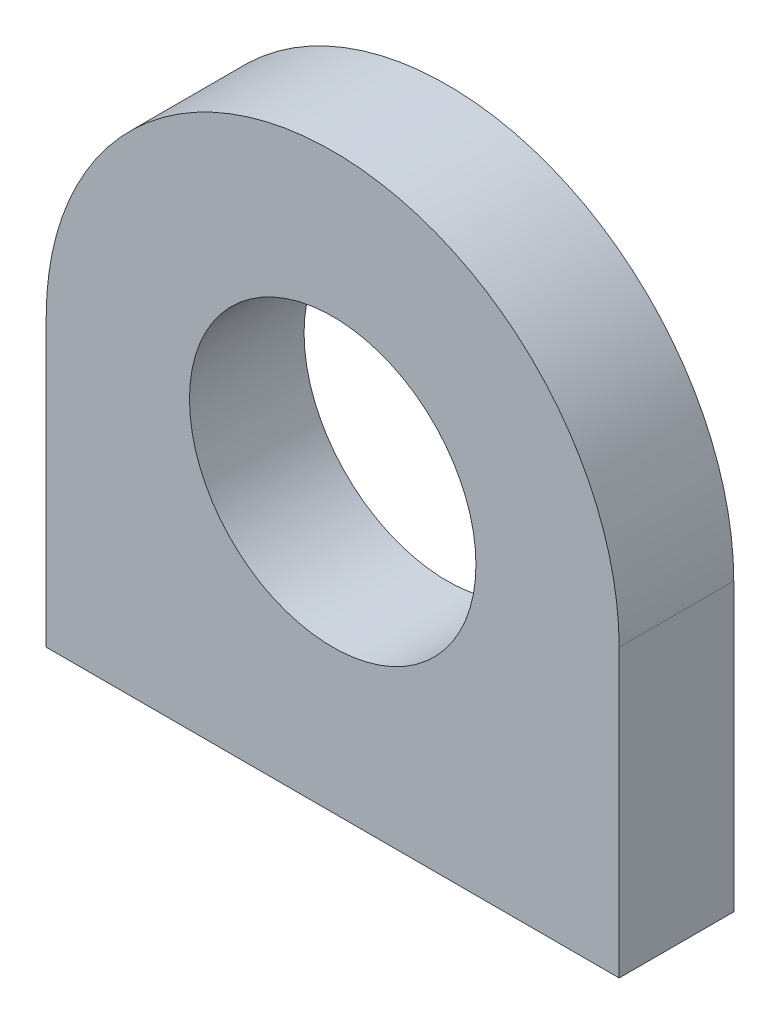
SolidWorks part; units mm, degrees
ref_plane "Front Plane" through (0, 0, 0) normal (0, 0, 1) x (1, 0, 0)
ref_plane "Top Plane" through (0, 0, 0) normal (0, 1, 0) x (1, 0, 0)
ref_plane "Right Plane" through (0, 0, 0) normal (1, 0, 0) x (0, 0, -1)
sketch "Sketch1" plane through (0, 0, 0) normal (0, 0, 1) x (1, 0, 0)
  line L1 (-10, -5) -> (10, -5)
  line L2 (-10, -5) -> (-10, 5)
  line L4 (10, -5) -> (10, 5)
  line L5 (-10, -5) -> (10, 5) construction
  line L6 (-10, 5) -> (10, -5) construction
  circle A0 centre (0, 5) radius 5
  arc A1 (10, 5) -> (-10, 5) centre (0, 5) ccw
  point P0 (0, 0)
extrude "Boss-Extrude1" add sketch "Sketch1" along normal blind 4
sketch "Sketch2" plane through (0, -5, 0) normal (0, -1, 0) x (1, 0, 0)
  line L1 (-10, 4) -> (-10, 0) construction
  circle A0 centre (-7, 2) radius 1
  circle A1 centre (7, 2) radius 1
  dimension "D1" = 14
  dimension "D2" = 3
extrude "Cut-Extrude1" cut sketch "Sketch2" against normal blind 4
